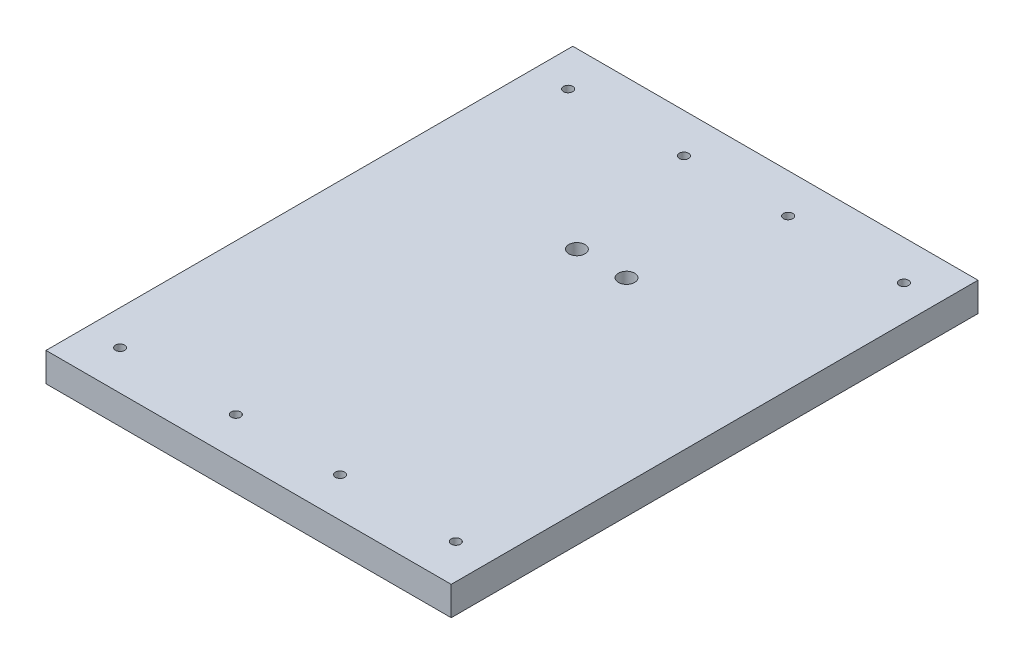
SolidWorks part; units mm, degrees
ref_plane "Front Plane" through (0, 0, 0) normal (0, 0, 1) x (1, 0, 0)
ref_plane "Top Plane" through (0, 0, 0) normal (0, 1, 0) x (1, 0, 0)
ref_plane "Right Plane" through (0, 0, 0) normal (1, 0, 0) x (0, 0, -1)
sketch "Sketch1" plane through (0, 0, 0) normal (0, 1, 0) x (1, 0, 0)
  line L1 (-44.45, -57.785) -> (44.45, -57.785)
  line L2 (-44.45, -57.785) -> (-44.45, 57.785)
  line L3 (-44.45, 57.785) -> (44.45, 57.785)
  line L4 (44.45, -57.785) -> (44.45, 57.785)
  line L5 (-44.45, -57.785) -> (44.45, 57.785) construction
  line L6 (-44.45, 57.785) -> (44.45, -57.785) construction
  point P0 (0, 0)
  dimension "D1" = 88.9
  dimension "D2" = 115.57
extrude "Boss-Extrude1" add sketch "Sketch1" along normal blind 6.35
sketch "Sketch2" plane through (0, 6.35, 0) normal (0, 1, 0) x (1, 0, 0)
  line L0 (-44.45, 57.785) -> (-44.45, -57.785) construction
  line L1 (44.45, -57.785) -> (44.45, 57.785) construction
  line L3 (44.45, 57.785) -> (-44.45, 57.785) construction
  line L4 (-44.45, 0) -> (44.45, 0) construction
  circle A0 centre (-36.83, 49.149) radius 1.016
  circle A1 centre (-11.43, 49.149) radius 1.016
  circle A2 centre (11.43, 49.149) radius 1.016
  circle A3 centre (36.83, 49.149) radius 1.016
  circle A4 centre (36.83, -49.149) radius 1.016
  circle A5 centre (-11.43, -49.149) radius 1.016
  circle A6 centre (11.43, -49.149) radius 1.016
  circle A7 centre (-36.83, -49.149) radius 1.016
  dimension "D1" = 2.032
  dimension "D2" = 2.032
  dimension "D3" = 2.032
  dimension "D4" = 2.032
  dimension "D5" = 7.62
  dimension "D6" = 25.4
  dimension "D7" = 7.62
  dimension "D8" = 25.4
  dimension "D9" = 8.636
extrude "Cut-Extrude1" cut sketch "Sketch2" against normal through all
sketch "Sketch4" plane through (0, 6.35, 0) normal (0, 1, 0) x (1, 0, 0)
  line L0 (44.45, 57.785) -> (-44.45, 57.785) construction
  line L1 (0, 57.785) -> (0, -57.785) construction
  line L2 (-44.45, -57.785) -> (44.45, -57.785) construction
  circle A0 centre (-5.445, 19.685) radius 1.778
  circle A1 centre (5.445, 19.685) radius 1.778
  dimension "D1" = 3.556
  dimension "D2" = 5.445
  dimension "D3" = 38.1
extrude "Cut-Extrude2" cut sketch "Sketch4" against normal through all
